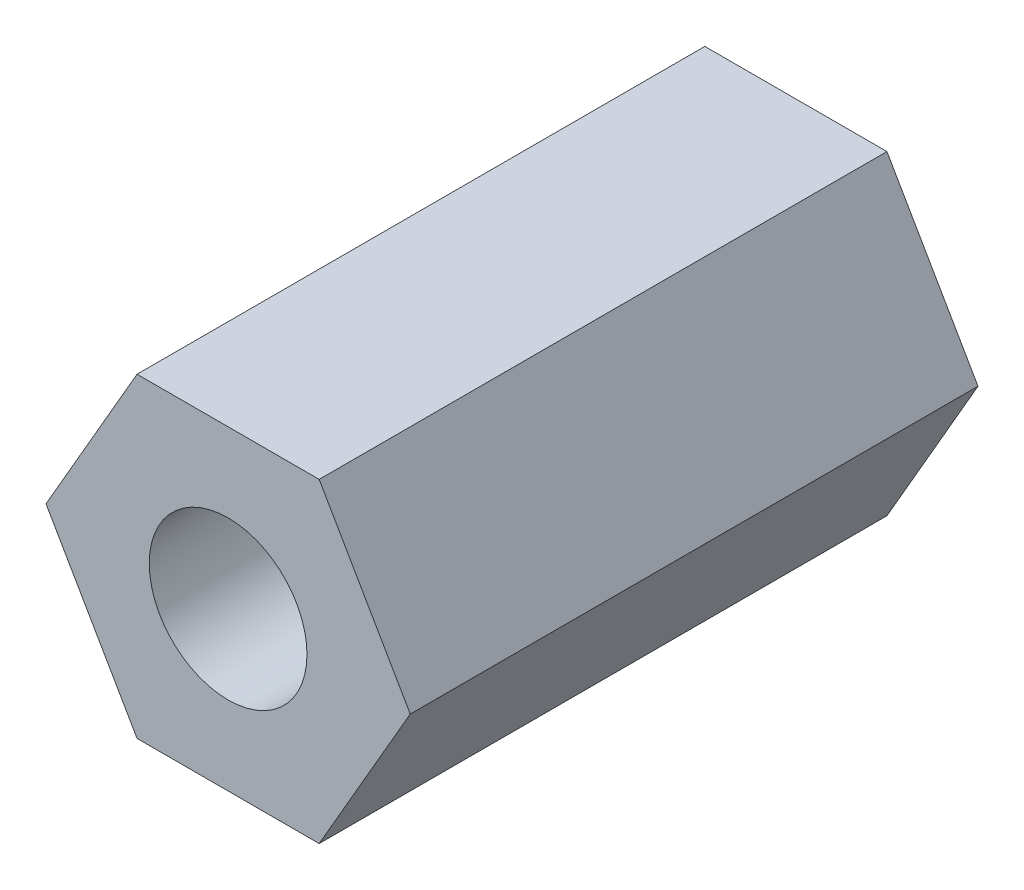
SolidWorks part; units mm, degrees
material "黃銅"
ref_plane "前基準面" through (0, 0, 0) normal (0, 0, 1) x (1, 0, 0)
ref_plane "上基準面" through (0, 0, 0) normal (0, 1, 0) x (1, 0, 0)
ref_plane "右基準面" through (0, 0, 0) normal (1, 0, 0) x (0, 0, -1)
sketch "草圖1" plane through (0, 0, 0) normal (0, 0, 1) x (1, 0, 0)
  line L1 (-1.4434, 2.5) -> (-2.8868, 0)
  line L2 (-2.8868, 0) -> (-1.4434, -2.5)
  line L3 (-1.4434, -2.5) -> (1.4434, -2.5)
  line L4 (1.4434, -2.5) -> (2.8868, 0)
  line L5 (2.8868, 0) -> (1.4434, 2.5)
  line L6 (1.4434, 2.5) -> (-1.4434, 2.5)
  circle A0 centre (0, 0) radius 2.5 construction
  dimension "D1" = 5
extrude "填料-伸長1" add sketch "草圖1" along normal blind 9
hole_wizard "M3x0.5 螺紋孔1" positions "草圖2" profile "草圖3" tap size "M3x0.5" standard "Ansi Metric" end condition through all
sketch "草圖2" plane through (0, 0, 9) normal (0, 0, 1) x (1, 0, 0)
  point P0 (0, 0)
sketch "草圖3" plane through (0, 0, 9) normal (1, 0, 0) x (0, -1, 0)
  line L0 (0, 0) -> (0, 9)
  line L1 (0, 9) -> (1.25, 9)
  line L2 (1.25, 9) -> (1.25, 0)
  line L5 (1.25, 0) -> (0, 0)
  line L11 (0, -6.35) -> (0, 107.95) construction
  dimension "貫穿螺孔鑽直徑" = 2.5
  dimension "貫穿螺孔鑽深度" = 9
